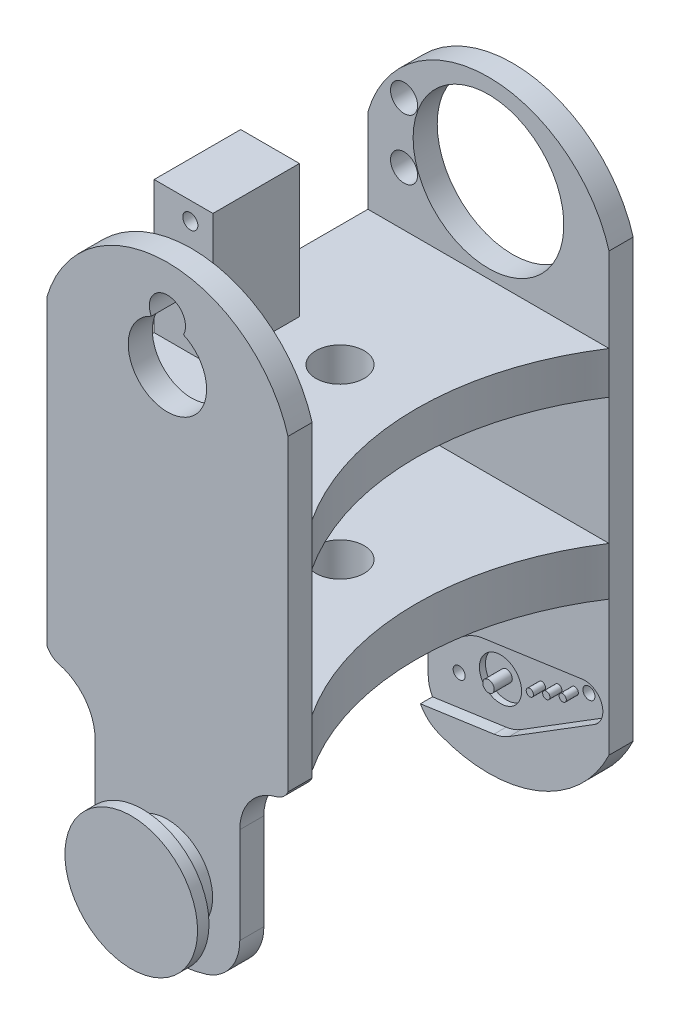
SolidWorks part; units mm, degrees
material "ABS"
ref_plane "Front Plane" through (0, 0, 0) normal (1, 0, 0) x (0, 1, 0)
ref_plane "Top Plane" through (0, 0, 0) normal (0, 0, 1) x (0, 1, 0)
ref_plane "Right Plane" through (0, 0, 0) normal (0, 1, 0) x (-1, 0, 0)
sketch "Sketch1" plane through (0, 0, 0) normal (1, 0, 0) x (0, 1, 0)
  line L0 (-12.5, 24.625) -> (-12.5, 28.625)
  line L1 (-12.5, -28.625) -> (87.5, -28.625)
  line L2 (-12.5, -28.625) -> (-12.5, -24.625)
  line L3 (-12.5, 28.625) -> (87.5, 28.625)
  line L4 (87.5, -28.625) -> (87.5, -24.625)
  line L5 (0, 19.4677) -> (0, -20.0323) construction
  line L7 (-12.5, 24.625) -> (22.5, 24.625)
  line L9 (-12.5, -24.625) -> (22.5, -24.625)
  line L11 (87.5, 24.625) -> (87.5, 28.625)
  line L16 (37.5, -971.625) -> (37.5, 49028.375) construction
  line L20 (22.5, 24.625) -> (22.5, -24.625)
  line L22 (30.5, 24.625) -> (30.5, -24.625)
  line L23 (30.5, 24.625) -> (51.5, 24.625)
  line L24 (30.5, -24.625) -> (51.5, -24.625)
  line L25 (58.5, 24.625) -> (58.5, -24.625)
  line L26 (51.5, 24.625) -> (51.5, -24.625)
  line L27 (58.5, 24.625) -> (87.5, 24.625)
  line L28 (58.5, -24.625) -> (87.5, -24.625)
  point P8 (37.5, 28.625)
  point P16 (22.5, 0)
  dimension "D1" = 49.25
  dimension "D2" = 100
  dimension "D3" = 8
  dimension "D4" = 7
  dimension "D5" = 12.5
  dimension "D6" = 7
  dimension "D7" = 4
  dimension "D8" = 14
  dimension "D20" = 0
extrude "Boss-Extrude1" add sketch "Sketch1" along normal mid plane 40
sketch "Sketch4" plane through (0, 0, -28.625) normal (0, 0, -1) x (1, 0, 0)
  circle A0 centre (0, 0) radius 7.5
  dimension "D1" = 15
extrude "Boss-Extrude2" add sketch "Sketch4" along normal blind 6 and the other way blind 63.25
sketch "Sketch2" plane through (0, 0, -28.625) normal (0, 0, -1) x (1, 0, 0)
  line L1 (-1000, 0) -> (49000, 0) construction
  line L11 (20, -0.0876) -> (20, -72.5)
  line L13 (-20, -0.0876) -> (-20, -72.5)
  line L14 (-975.8579, -36.2938) -> (49024.1421, -36.2938) construction
  line L15 (-977.5, -72.5) -> (49022.5, -72.5) construction
  line L16 (-25, 19.9124) -> (25, 19.9124)
  line L17 (-25, 19.9124) -> (-25, -92.5)
  line L18 (-25, -92.5) -> (25, -92.5)
  line L19 (25, 19.9124) -> (25, -92.5)
  line L269 (0, -987.5) -> (0, 49012.5) construction
  line L272 (-20, -41.6571) -> (20, -41.6571) construction
  line L276 (20, -87.5) -> (-20, -87.5) construction
  line L277 (20, 12.5) -> (20, -87.5) construction
  line L278 (20, 12.5) -> (-20, 12.5) construction
  arc A22 (20, -0.0876) -> (-20, -0.0876) centre (0, -9.6825) ccw
  circle A25 centre (0, -72.5) radius 12.5
  arc A26 (-20, -72.5) -> (20, -72.5) centre (0, -66.6667) ccw
  point P11 (-20, -87.5)
  point P16 (20, 12.5)
  point P18 (0, -41.6571)
  point P24 (25, -36.2938)
  dimension "D3" = 72.5
  dimension "D4" = 15
  dimension "D5" = 5
  dimension "D10" = 9.6825
  dimension "D11" = 25
  dimension "D6" = 5
  dimension "D8" = 5
extrude "Cut-Extrude1" cut sketch "Sketch2" against normal through all both and the other way through all
sketch "Sketch5" plane through (20, 0, 0) normal (1, 0, 0) x (0, 1, 0)
  line L1 (-10, -24.625) -> (10, -24.625)
  line L2 (-10, -24.625) -> (-10, 24.625)
  line L3 (-10, 24.625) -> (10, 24.625)
  line L4 (10, -24.625) -> (10, 24.625)
  line L5 (0, 24.625) -> (0, -24.625) construction
  line L6 (-10, 0) -> (10, 0) construction
  line L9 (0.0876, 24.625) -> (22.5, 24.625) construction
  point P0 (0, 0)
  dimension "D1" = 20
extrude "Cut-Extrude2" cut sketch "Sketch5" against normal through all
sketch "Sketch6" plane through (0, 0, -28.625) normal (0, 0, -1) x (1, 0, 0)
  line L0 (-1000, 0) -> (49000, 0) construction
  line L1 (0, -1000) -> (0, 49000) construction
  line L2 (-20, 17) -> (-20, -13.0483) construction
  line L3 (-12, 5.3436) -> (-12, -13.0483)
  line L5 (-20, -0.0876) -> (-20, -72.5) construction
  line L6 (0, 12.5) -> (0, 15.4182)
  line L7 (0, 15.4182) -> (-20, 15.4182)
  line L8 (-989.1028, -36.25) -> (49010.8972, -36.25) construction
  line L11 (-20, 15.4182) -> (-20, -22.5)
  line L12 (-1015.3374, -21.0483) -> (48984.6626, -21.0483) construction
  arc A5 (-18, -20.7942) -> (-12, -13.0483) centre (-20, -13.0483) ccw
  arc A6 (0, 12.5) -> (-8.2209, 10.9204) centre (0, -9.6825) ccw
  arc A7 (20, -0.0876) -> (-20, -0.0876) centre (0, -9.6825) ccw construction
  arc A8 (-8.2209, 10.9204) -> (-12, 5.3436) centre (-5.9956, 5.3436) ccw
  arc A9 (-18, -20.7942) -> (-20, -22.5) centre (-17.25, -23.699) ccw
  point P5 (-17.5, 0)
  dimension "D3" = 37.9182
  dimension "D1" = 12
  dimension "D2" = 6.0044
  dimension "D5" = 3
  dimension "D4" = 36.25
  dimension "D6" = 2
extrude "Cut-Extrude3" cut sketch "Sketch6" against normal through all
sketch "Sketch7" plane through (0, 58.5, 0) normal (0, 1, 0) x (-1, 0, 0)
  line L0 (10.25, -3.525) -> (20, -3.525)
  line L1 (10.25, -3.525) -> (10.25, 10.825)
  line L2 (10.25, 10.825) -> (20, 10.825)
  line L3 (20, -3.525) -> (20, 10.825)
  line L6 (-20, 24.625) -> (20, 24.625) construction
  line L9 (20, -24.625) -> (-20, -24.625) construction
  line L11 (20, -24.625) -> (20, 24.625) construction
  point P0 (11.2346, 1.7073)
  dimension "D2" = 13.8
  dimension "D3" = 10.25
  dimension "D4" = 21.1
extrude "Boss-Extrude3" add sketch "Sketch7" along normal blind 22
sketch "Sketch8" plane through (0, 0, -3.525) normal (0, 0, -1) x (1, 0, 0)
  line L0 (-14, -1066.1184) -> (-14, 48933.8816) construction
  line L1 (0, -1000) -> (0, 49000) construction
  line L2 (-997, -72.5) -> (49003, -72.5) construction
  circle A0 centre (0, -72.5) radius 12.5 construction
  circle A1 centre (0, -72.5) radius 12.5 construction
  circle A2 centre (-14, -67.5) radius 1.25
  circle A3 centre (-14, -77.5) radius 1.25
  dimension "D2" = 2.5
  dimension "D1" = 14
  dimension "D3" = 5
extrude "Cut-Extrude4" cut sketch "Sketch8" against normal up to next
sketch "Sketch9" plane through (0, 0, -28.625) normal (0, 0, -1) x (1, 0, 0)
  line L0 (-1006.5, -72.5) -> (48993.5, -72.5) construction
  circle A1 centre (-14, -77.5) radius 2.25
  circle A2 centre (-14, -77.5) radius 1.25 construction
  circle A3 centre (-14, -67.5) radius 2.25
  dimension "D1" = 4.5
  dimension "D2" = 5
  dimension "D3" = 10
extrude "Cut-Extrude5" cut sketch "Sketch9" against normal blind 26.4
sketch "Sketch10" plane through (0, 0, -24.625) normal (0, 0, 1) x (1, 0, 0)
  line L0 (-18.7939, -6.8404) -> (18.7939, 6.8404) construction
  line L1 (-2.9286, 8.0463) -> (17098.0785, -46976.5847) construction
  line L2 (-1000, 0) -> (49000, 0) construction
  line L3 (15.2752, 16.5077) -> (17116.2824, -46968.1234) construction
  line L4 (-0.918, 6.4349) -> (15.5511, 8.7843)
  line L5 (3.433, -5.5194) -> (17.5593, 3.2669)
  line L6 (0.918, -6.4349) -> (-15.5511, -8.7843)
  line L7 (-3.433, 5.5194) -> (-17.5593, -3.2669)
  line L8 (-7.9121, 2.7335) -> (-4.3039, -7.1798) construction
  circle A0 centre (0, 0) radius 3.5 construction
  arc A1 (-0.918, 6.4349) -> (-3.433, 5.5194) centre (0, 0) ccw
  arc A2 (17.5593, 3.2669) -> (15.5511, 8.7843) centre (15.9748, 5.8143) ccw
  circle A3 centre (15.0351, 5.4723) radius 0.6 construction
  circle A4 centre (12.31, 4.4805) radius 0.6
  circle A5 centre (9.5849, 3.4886) radius 0.6
  circle A6 centre (6.8598, 2.4967) radius 0.6
  circle A7 centre (0, 0) radius 0.95
  arc A8 (-15.5511, -8.7843) -> (-17.5593, -3.2669) centre (-15.9748, -5.8143) cw
  circle A9 centre (-6.8598, -2.4967) radius 0.6 construction
  arc A10 (0.918, -6.4349) -> (3.433, -5.5194) centre (0, 0) ccw
  circle A11 centre (0, 0) radius 6.5 construction
  point P9 (0, 0)
  dimension "D1" = 7
  dimension "D2" = 13
  dimension "D5" = 6
  dimension "D10" = 1.2
  dimension "D11" = 1.9
  dimension "D3" = 20
  dimension "D4" = 20
  dimension "D6" = 16
  dimension "D7" = 2.9
  dimension "D8" = 2.9
  dimension "D9" = 7.3
extrude "Cut-Extrude6" cut sketch "Sketch10" against normal blind 2
sketch "Sketch17" plane through (0, 0, -26.625) normal (0, 0, 1) x (1, 0, 0)
  circle A0 centre (0, 0) radius 3.5
  circle A4 centre (0, 0) radius 0.95
  circle A5 centre (0, 0) radius 0.95 construction
  dimension "D1" = 7
extrude "Cut-Extrude11" cut sketch "Sketch17" against normal blind 1
sketch "Sketch11" plane through (0, 0, -26.625) normal (0, 0, 1) x (1, 0, 0)
  line L0 (0, 0) -> (15.9748, 5.8143) construction
  line L1 (-1.801, 4.9482) -> (17099.2062, -46979.6828) construction
  circle A0 centre (14.6592, 5.3355) radius 1
  circle A1 centre (12.31, 4.4805) radius 0.6 construction
  circle A2 centre (6.8598, 2.4967) radius 1 construction
  circle A3 centre (6.8598, 2.4967) radius 0.6 construction
  circle A4 centre (-6.8598, -2.4967) radius 1
  dimension "D2" = 2
  dimension "D1" = 2.5
extrude "Cut-Extrude7" cut sketch "Sketch11" against normal up to surface (2 mm away) up to face at (-16.25, 77.5, -28.625)
sketch "Sketch12" plane through (0, 0, 28.625) normal (0, 0, 1) x (1, 0, 0)
  line L0 (-1016.1491, 20) -> (48983.8509, 20) construction
  line L9 (0, -1000.069) -> (0, 1000.069) construction
  line L22 (0, -12.5) -> (0, -18.0391)
  line L23 (0, -18.0391) -> (20, -18.0391)
  line L25 (12, -3.926) -> (12, 12)
  line L26 (20, 21.4291) -> (20, -18.0391)
  line L29 (20, 72.5) -> (20, 0.0876) construction
  arc A12 (0, -12.5) -> (6.4502, -11.5415) centre (0.3247, 7.4974) ccw
  arc A13 (18.0082, 19.7481) -> (12, 12) centre (20, 12) ccw
  arc A14 (6.4502, -11.5415) -> (12, -3.926) centre (4, -3.926) ccw
  arc A15 (-8.2209, -10.9204) -> (20, 0.0876) centre (0, 9.6825) ccw construction
  circle A16 centre (0, 0) radius 7.5 construction
  arc A17 (20, 21.4291) -> (18.0082, 19.7481) centre (17.2613, 22.6536) cw
  dimension "D1" = 8
  dimension "D4" = 20
  dimension "D7" = 1.9918
  dimension "D5" = 8
  dimension "D6" = 20
  dimension "D3" = 3
  dimension "D2" = 5.5391
extrude "Cut-Extrude8" cut sketch "Sketch12" against normal blind 4
sketch "Sketch13" plane through (0, 58.5, 0) normal (0, 1, 0) x (-1, 0, 0)
  line L0 (-20, 24.625) -> (-20, -24.625)
  line L1 (-20, -24.625) -> (20, -24.625) construction
  line L2 (-20, 24.625) -> (20, 24.625) construction
  line L6 (-20, -24.625) -> (-20, 24.625) construction
  arc A0 (-20, -24.625) -> (-20, 24.625) centre (-57.6644, 0) ccw
  dimension "D1" = 90
extrude "Cut-Extrude9" cut sketch "Sketch13" against normal through all
sketch "Sketch14" plane through (0, 0, 28.625) normal (0, 0, 1) x (1, 0, 0)
  circle A0 centre (0, 72.5) radius 12.5
  circle A1 centre (0, 72.5) radius 6.5
  circle A2 centre (0, 72.5) radius 12.5 construction
  dimension "D1" = 13
extrude "Boss-Extrude4" add sketch "Sketch14" against normal up to surface (4 mm away) up to face at (12.5, 72.5, 24.625)
sketch "Sketch16" plane through (0, 0, 28.625) normal (0, 0, 1) x (1, 0, 0)
  line L4 (-1000, 72.5) -> (49000, 72.5) construction
  line L9 (-1001.5159, 79.8) -> (48998.4841, 79.8) construction
  line L10 (0, -1000) -> (0, 49000) construction
  circle A8 centre (0, 79.8) radius 3
  dimension "D2" = 6
  dimension "D1" = 7.3
extrude "Cut-Extrude10" cut sketch "Sketch16" against normal up to surface (4 mm away) up to face at (0, 69.25, 24.625)
sketch "Sketch18" plane through (0, 0, 34.625) normal (0, 0, 1) x (1, 0, 0)
  circle A0 centre (0, 0) radius 11
  dimension "D1" = 22
extrude "Boss-Extrude5" add sketch "Sketch18" against normal blind 1.9
sketch "Sketch19" plane through (0, 0, -34.625) normal (0, 0, -1) x (1, 0, 0)
  circle A0 centre (0, 0) radius 11
  dimension "D1" = 22
extrude "Boss-Extrude6" add sketch "Sketch19" against normal blind 1.9
sketch "Sketch20" plane through (0, 22.5, 0) normal (0, -1, 0) x (1, 0, 0)
  circle A0 centre (0, 0) radius 4
  dimension "D1" = 8
extrude "Cut-Extrude12" cut sketch "Sketch20" against normal blind 75
sketch "Sketch22" plane through (0, 22.5, 0) normal (0, -1, 0) x (1, 0, 0)
  circle A0 centre (-57.6644, 0) radius 45
  arc A1 (20, 24.625) -> (20, -24.625) centre (57.6644, 0) ccw construction
extrude "Cut-Extrude14" cut sketch "Sketch22" against normal up to surface (8 mm away) up to face at (0, 30.5, 4)
